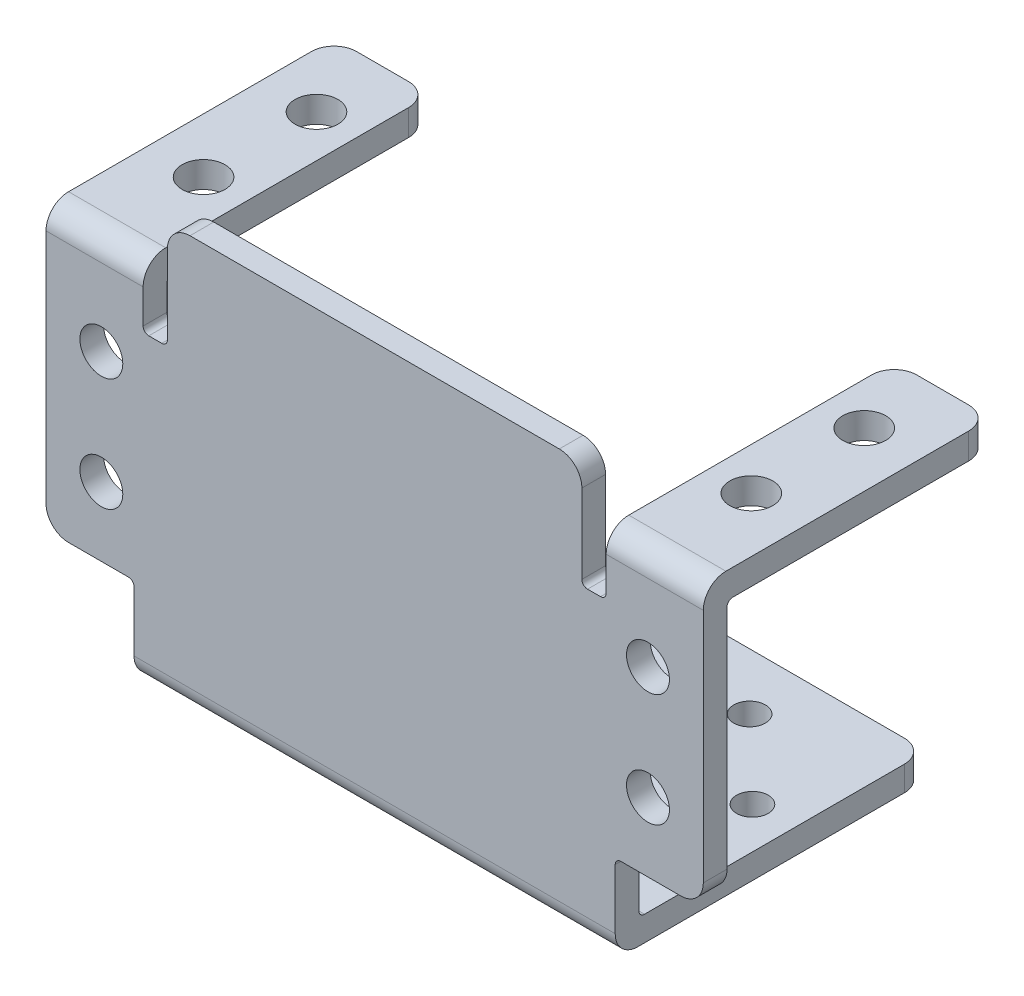
SolidWorks part; units mm, degrees
ref_plane "Front Plane" through (0, 0, 0) normal (0, 0, 1) x (1, 0, 0)
ref_plane "Top Plane" through (0, 0, 0) normal (0, 1, 0) x (1, 0, 0)
ref_plane "Right Plane" through (0, 0, 0) normal (1, 0, 0) x (0, 0, -1)
sketch "Sketch1" plane through (0, 0, 0) normal (1, 0, 0) x (0, 0, -1)
  line L2 (0, 0) -> (0, 36.7)
  line L8 (27.6, 0) -> (27.6, 2.2)
  line L9 (2.1, 2.2) -> (27.6, 2.2)
  line L10 (0, 0) -> (27.6, 0)
  line L11 (0, 36.7) -> (25.5, 36.7)
  line L12 (25.5, 36.7) -> (25.5, 30.4)
  line L13 (25.5, 30.4) -> (2.1, 30.4)
  line L14 (2.1, 30.4) -> (2.1, 2.2)
  dimension "D1" = 36.7
  dimension "D2" = 27.6
  dimension "D3" = 2.2
  dimension "D4" = 25.5
  dimension "D5" = 6.3
  dimension "D6" = 2.1
extrude "Boss-Extrude1" add sketch "Sketch1" along normal mid plane 58.2
sketch "Sketch2" plane through (0, 36.7, 0) normal (0, 1, 0) x (1, 0, 0)
  line L0 (-29.1, 2.1) -> (29.1, 2.1) construction
  line L1 (-29.1, 25.5) -> (-29.1, 0) construction
  line L2 (29.1, 25.5) -> (29.1, 0) construction
  line L3 (29.1, 0) -> (-29.1, 0) construction
  line L4 (-18.35, 2.1) -> (18.35, 2.1)
  line L5 (-18.35, 2.1) -> (-18.35, 0)
  line L6 (-18.35, 0) -> (-20.5, 0)
  line L7 (-20.5, 0) -> (-20.5, 25.5)
  line L8 (29.1, 25.5) -> (-29.1, 25.5) construction
  line L9 (-20.5, 25.5) -> (20.5, 25.5)
  line L10 (18.35, 2.1) -> (18.35, 0)
  line L11 (18.35, 0) -> (20.5, 0)
  line L12 (20.5, 0) -> (20.5, 25.5)
  point P11 (0, 2.1)
  dimension "D1" = 2.1
  dimension "D2" = 36.7
  dimension "D3" = 2.15
  dimension "D4" = 2.15
extrude "Cut-Extrude1" cut sketch "Sketch2" against normal blind 9.5
sketch "Sketch3" plane through (0, 36.7, 0) normal (0, 1, 0) x (1, 0, 0)
  line L1 (29.1, 0) -> (20.5, 0)
  line L2 (29.1, 0) -> (29.1, 25.5)
  line L3 (29.1, 25.5) -> (20.5, 25.5)
  line L4 (20.5, 0) -> (20.5, 25.5)
  line L5 (-20.5, 0) -> (-29.1, 0)
  line L6 (-20.5, 0) -> (-20.5, 25.5)
  line L7 (-20.5, 25.5) -> (-29.1, 25.5)
  line L8 (-29.1, 0) -> (-29.1, 25.5)
extrude "Cut-Extrude2" cut sketch "Sketch3" against normal blind 4
sketch "Sketch4" plane through (0, 0, 0) normal (0, -1, 0) x (1, 0, 0)
  line L1 (-29.1, 0) -> (-21.3, 0)
  line L2 (-29.1, 0) -> (-29.1, -27.6)
  line L3 (-29.1, -27.6) -> (-21.3, -27.6)
  line L4 (-21.3, 0) -> (-21.3, -27.6)
  line L5 (29.1, -27.6) -> (-29.1, -27.6) construction
  line L7 (29.1, 0) -> (21.3, 0)
  line L8 (29.1, 0) -> (29.1, -27.6)
  line L9 (29.1, -27.6) -> (21.3, -27.6)
  line L10 (21.3, 0) -> (21.3, -27.6)
  dimension "D1" = 27.6
  dimension "D2" = 7.8
  dimension "D3" = 27.6
  dimension "D4" = 7.8
extrude "Cut-Extrude3" cut sketch "Sketch4" against normal blind 7.8
sketch "Sketch5" plane through (0, 32.7, 0) normal (0, 1, 0) x (1, 0, 0)
  line L0 (-20.5, 12.75) -> (20.5, 12.75) construction
  line L1 (-20.5, 0) -> (-20.5, 25.5) construction
  line L2 (20.5, 25.5) -> (20.5, 0) construction
  line L3 (0, 12.75) -> (0, 33.6303) construction
  line L4 (-24.25, 17.2) -> (-24.25, 11) construction
  line L5 (-22.35, 19.1) -> (-20.5, 19.1) construction
  line L6 (-24.25, 21) -> (-24.25, 25.5) construction
  line L7 (-20.5, 25.5) -> (-29.1, 25.5) construction
  circle A0 centre (-24.25, 19.1) radius 1.9
  circle A1 centre (-24.25, 9.1) radius 1.9
  circle A2 centre (24.25, 9.1) radius 1.9
  circle A3 centre (24.25, 19.1) radius 1.9
  dimension "D1" = 3.8
  dimension "D5" = 3.8
  dimension "D2" = 6.2
  dimension "D3" = 1.85
  dimension "D4" = 4.5
extrude "Cut-Extrude4" cut sketch "Sketch5" against normal up to surface (2.3 mm away) up to face at (-24.8, 30.4, -13.8)
sketch "Sketch6" plane through (0, 0, 0) normal (0, 0, 1) x (1, 0, 0)
  line L0 (-29.1, 20.25) -> (29.1, 20.25) construction
  line L1 (-29.1, 32.7) -> (-29.1, 7.8) construction
  line L2 (29.1, 32.7) -> (29.1, 7.8) construction
  line L3 (0, 20.25) -> (0, 39.9775) construction
  line L4 (24.2, 22) -> (24.2, 15.8) construction
  line L5 (24.2, 12) -> (24.2, 7.8) construction
  line L6 (29.1, 7.8) -> (21.3, 7.8) construction
  line L7 (26.1, 13.9) -> (29.1, 13.9) construction
  circle A0 centre (24.2, 23.9) radius 1.9
  circle A1 centre (24.2, 13.9) radius 1.9
  circle A2 centre (-24.2, 13.9) radius 1.9
  circle A3 centre (-24.2, 23.9) radius 1.9
  dimension "D1" = 3.8
  dimension "D4" = 3.8
  dimension "D2" = 6.2
  dimension "D3" = 4.2
  dimension "D5" = 3
extrude "Cut-Extrude5" cut sketch "Sketch6" against normal up to surface (2.1 mm away) up to face at (0, 21.2125, -2.1)
fillet "Fillet 2mm" radius 2 13 edges at (-24.8, 32.7, 0) (21.3, 1.1, -27.6) (-21.3, 1.1, -27.6) (0, 0, 0) (29.1, 7.8, -1.05) (-29.1, 7.8, -1.05) (29.1, 31.55, -25.5) (20.5, 31.55, -25.5) (-20.5, 31.55, -25.5) (-29.1, 31.55, -25.5) (24.8, 32.7, 0) (18.35, 36.7, -1.05) (-18.35, 36.7, -1.05)
fillet "Fillet2" radius 0.5 9 edges at (-18.35, 27.2, -1.05) (-20.5, 27.2, -1.05) (18.35, 27.2, -1.05) (20.5, 27.2, -1.05) (21.3, 7.8, -1.05) (-21.3, 7.8, -1.05) (24.8, 30.4, -2.1) (-24.8, 30.4, -2.1) (0, 2.2, -2.1)
sketch "Sketch7" plane through (0, 2.2, 0) normal (0, 1, 0) x (1, 0, 0)
  line L0 (19.05, 15.8) -> (21.3, 15.8) construction
  line L1 (21.3, 2.6) -> (21.3, 25.6) construction
  line L2 (10.6, 14.4) -> (10.6, 10.4) construction
  line L3 (9.2, 15.8) -> (4.95, 15.8) construction
  line L4 (10.6, 21.2) -> (10.6, 17.2) construction
  line L5 (12, 15.8) -> (16.25, 15.8) construction
  line L6 (0, 27.6) -> (0, 3.1183) construction
  line L7 (19.3, 27.6) -> (-19.3, 27.6) construction
  line L8 (2.15, 15.8) -> (0, 15.8) construction
  line L9 (10.6, 24) -> (10.6, 27.6) construction
  line L10 (-12, 15.8) -> (-16.25, 15.8) construction
  line L11 (-10.6, 21.2) -> (-10.6, 17.2) construction
  line L12 (-9.2, 15.8) -> (-4.95, 15.8) construction
  line L13 (-10.6, 14.4) -> (-10.6, 10.4) construction
  circle A0 centre (10.6, 22.6) radius 1.4
  circle A1 centre (10.6, 9) radius 1.4
  circle A2 centre (10.6, 15.8) radius 1.4
  circle A3 centre (3.55, 15.8) radius 1.4
  circle A4 centre (17.65, 15.8) radius 1.4
  circle A5 centre (-17.65, 15.8) radius 1.4
  circle A6 centre (-3.55, 15.8) radius 1.4
  circle A7 centre (-10.6, 15.8) radius 1.4
  circle A8 centre (-10.6, 9) radius 1.4
  circle A9 centre (-10.6, 22.6) radius 1.4
  dimension "D1" = 2.8
  dimension "D2" = 2.8
  dimension "D3" = 2.8
  dimension "D4" = 2.8
  dimension "D5" = 2.8
  dimension "D6" = 4
  dimension "D7" = 4
  dimension "D8" = 4.25
  dimension "D9" = 4.25
  dimension "D10" = 2.25
  dimension "D11" = 3.6
extrude "Cut-Extrude6" cut sketch "Sketch7" against normal up to surface (2.2 mm away) up to face at (0, 0, -18.5381)
